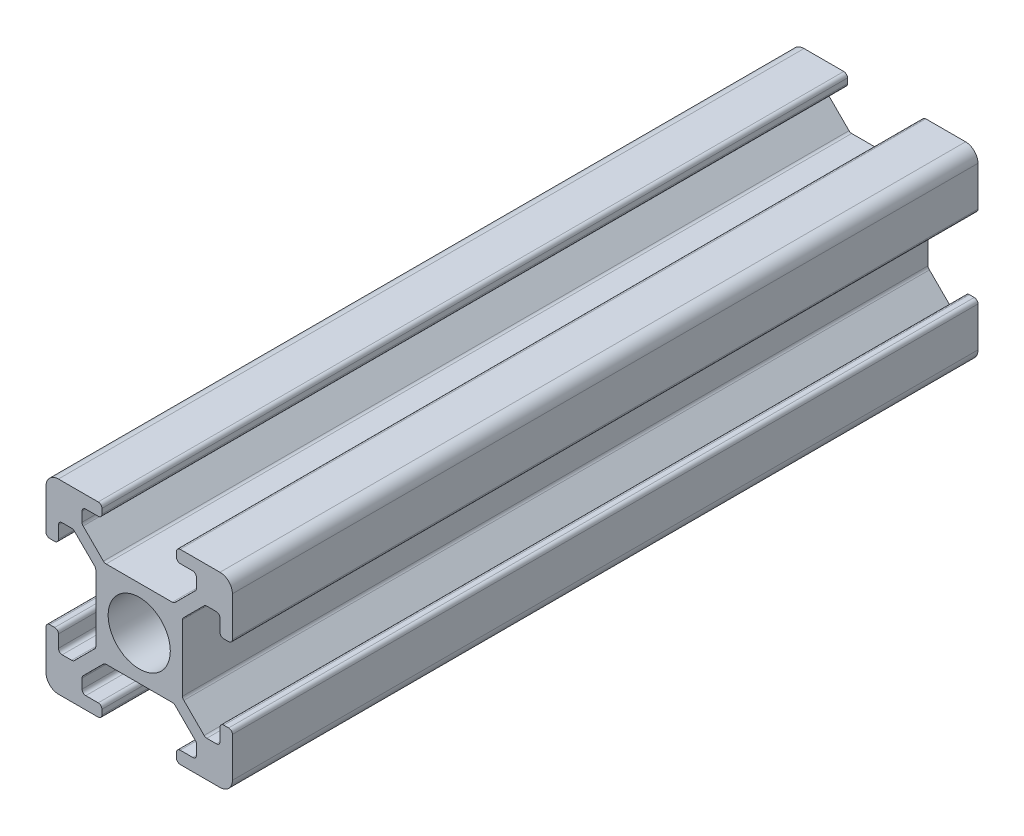
SolidWorks part; units mm, degrees
ref_plane "Front Plane" through (0, 0, 0) normal (0, 0, 1) x (1, 0, 0)
ref_plane "Top Plane" through (0, 0, 0) normal (0, 1, 0) x (1, 0, 0)
ref_plane "Right Plane" through (0, 0, 0) normal (1, 0, 0) x (0, 0, -1)
sketch "Sketch1" plane through (0, 0, 0) normal (0, 0, 1) x (1, 0, 0)
  line L0 (0.9971, -0.011) -> (4.1971, -0.011)
  line L1 (14.9971, 0.989) -> (14.9971, 4.189)
  line L2 (13.9971, 14.989) -> (10.7971, 14.989)
  line L3 (-0.0029, 13.989) -> (-0.0029, 10.789)
  line L4 (4.4971, 0.289) -> (4.4971, 0.689)
  line L5 (10.4971, 0.289) -> (10.4971, 0.689)
  line L6 (4.4971, 14.689) -> (4.4971, 14.289)
  line L7 (10.4971, 14.689) -> (10.4971, 14.289)
  line L8 (4.1971, 14.989) -> (0.9971, 14.989)
  line L9 (10.7971, -0.011) -> (13.9971, -0.011)
  line L10 (0.9971, 4.189) -> (0.9971, 3.189)
  line L11 (0.9971, 10.789) -> (0.9971, 11.7902)
  line L12 (14.6971, 10.5) -> (14.3, 10.5)
  line L13 (14.6971, 4.489) -> (14.3053, 4.489)
  line L14 (0.2971, 4.489) -> (0.6971, 4.489)
  line L15 (0.2971, 10.489) -> (0.6971, 10.489)
  line L16 (-0.0029, 4.189) -> (-0.0029, 0.989)
  line L17 (14.9971, 10.8) -> (14.9971, 13.989)
  line L18 (14, 10.8) -> (14, 11.8)
  line L19 (14.0053, 4.189) -> (14.0053, 3.189)
  line L20 (4.8302, 10.985) -> (10.1675, 10.985)
  line L21 (10.9699, 10.1634) -> (10.9699, 4.8261)
  line L22 (10.1715, 3.9947) -> (4.8343, 3.9947)
  line L23 (4.0029, 4.8261) -> (4.0029, 10.1634)
  line L24 (4.1971, 13.989) -> (3.1971, 13.989)
  line L25 (10.7971, 13.989) -> (11.7988, 13.989)
  line L26 (4.1971, 0.989) -> (3.1971, 0.989)
  line L27 (10.7971, 0.989) -> (11.8086, 0.989)
  line L28 (1.2971, 12.0902) -> (2.0579, 12.0902)
  line L29 (2.8971, 13.689) -> (2.8971, 12.9204)
  line L30 (1.2971, 2.889) -> (2.0658, 2.889)
  line L31 (2.8971, 1.289) -> (2.8971, 2.0576)
  line L32 (4.6181, 11.0728) -> (2.9867, 12.7042)
  line L33 (3.9121, 10.3808) -> (2.2729, 12.0018)
  line L34 (10.3796, 11.0728) -> (12.011, 12.7042)
  line L35 (11.0879, 10.3808) -> (12.7192, 12.0121)
  line L36 (11.0891, 4.6099) -> (12.7204, 2.9786)
  line L37 (10.3877, 3.9052) -> (12.0191, 2.2738)
  line L38 (4.6181, 3.9052) -> (2.9867, 2.2738)
  line L39 (3.9133, 4.6099) -> (2.282, 2.9786)
  line L40 (12.0988, 13.689) -> (12.0988, 12.9163)
  line L41 (13.7, 12.1) -> (12.9314, 12.1)
  line L42 (13.7053, 2.889) -> (12.9366, 2.889)
  line L43 (12.1086, 1.289) -> (12.1086, 2.0576)
  circle A0 centre (7.5, 7.5) radius 2.5
  arc A1 (0.9971, -0.011) -> (-0.0029, 0.989) centre (0.9971, 0.989) cw
  arc A2 (13.9971, -0.011) -> (14.9971, 0.989) centre (13.9971, 0.989) ccw
  arc A3 (14.9971, 13.989) -> (13.9971, 14.989) centre (13.9971, 13.989) ccw
  arc A4 (0.9971, 14.989) -> (-0.0029, 13.989) centre (0.9971, 13.989) ccw
  arc A5 (10.4971, 0.289) -> (10.7971, -0.011) centre (10.7971, 0.289) ccw
  arc A6 (10.4971, 0.689) -> (10.7971, 0.989) centre (10.7971, 0.689) cw
  arc A7 (4.4971, 0.289) -> (4.1971, -0.011) centre (4.1971, 0.289) cw
  arc A8 (4.4971, 0.689) -> (4.1971, 0.989) centre (4.1971, 0.689) ccw
  arc A9 (0.6971, 4.489) -> (0.9971, 4.189) centre (0.6971, 4.189) cw
  arc A10 (0.2971, 4.489) -> (-0.0029, 4.189) centre (0.2971, 4.189) ccw
  arc A11 (0.6971, 10.489) -> (0.9971, 10.789) centre (0.6971, 10.789) ccw
  arc A12 (0.2971, 10.489) -> (-0.0029, 10.789) centre (0.2971, 10.789) cw
  arc A13 (4.4971, 14.289) -> (4.1971, 13.989) centre (4.1971, 14.289) cw
  arc A14 (4.1971, 14.989) -> (4.4971, 14.689) centre (4.1971, 14.689) cw
  arc A15 (10.4971, 14.289) -> (10.7971, 13.989) centre (10.7971, 14.289) ccw
  arc A16 (10.7971, 14.989) -> (10.4971, 14.689) centre (10.7971, 14.689) ccw
  arc A17 (14.3053, 4.489) -> (14.0053, 4.189) centre (14.3053, 4.189) ccw
  arc A18 (14.9971, 4.189) -> (14.6971, 4.489) centre (14.6971, 4.189) ccw
  arc A19 (14.3, 10.5) -> (14, 10.8) centre (14.3, 10.8) cw
  arc A20 (14.9971, 10.8) -> (14.6971, 10.5) centre (14.6971, 10.8) cw
  arc A21 (11.7988, 13.989) -> (12.0988, 13.689) centre (11.7988, 13.689) cw
  arc A22 (14, 11.8) -> (13.7, 12.1) centre (13.7, 11.8) ccw
  arc A23 (14.0053, 3.189) -> (13.7053, 2.889) centre (13.7053, 3.189) cw
  arc A24 (11.8086, 0.989) -> (12.1086, 1.289) centre (11.8086, 1.289) ccw
  arc A25 (3.1971, 0.989) -> (2.8971, 1.289) centre (3.1971, 1.289) cw
  arc A26 (0.9971, 3.189) -> (1.2971, 2.889) centre (1.2971, 3.189) ccw
  arc A27 (0.9971, 11.7902) -> (1.2971, 12.0902) centre (1.2971, 11.7902) cw
  arc A28 (3.1971, 13.989) -> (2.8971, 13.689) centre (3.1971, 13.689) ccw
  arc A29 (10.3796, 11.0728) -> (10.1675, 10.985) centre (10.1675, 11.285) cw
  arc A30 (12.0988, 12.9163) -> (12.011, 12.7042) centre (11.7988, 12.9163) cw
  arc A31 (4.6181, 11.0728) -> (4.8302, 10.985) centre (4.8302, 11.285) ccw
  arc A32 (12.9314, 12.1) -> (12.7192, 12.0121) centre (12.9314, 11.8) ccw
  arc A33 (10.9699, 10.1634) -> (11.0879, 10.3808) centre (11.2692, 10.1417) cw
  arc A34 (11.0891, 4.6099) -> (10.9699, 4.8261) centre (11.269, 4.85) cw
  arc A35 (12.9366, 2.889) -> (12.7204, 2.9786) centre (12.9366, 3.1947) cw
  arc A36 (12.1086, 2.0576) -> (12.0191, 2.2738) centre (11.8029, 2.0576) ccw
  arc A37 (2.8971, 2.0576) -> (2.9867, 2.2738) centre (3.2029, 2.0576) cw
  arc A38 (10.3877, 3.9052) -> (10.1715, 3.9947) centre (10.1715, 3.689) ccw
  arc A39 (4.6181, 3.9052) -> (4.8343, 3.9947) centre (4.8343, 3.689) cw
  arc A40 (2.0658, 2.889) -> (2.282, 2.9786) centre (2.0658, 3.1947) ccw
  arc A41 (3.9133, 4.6099) -> (4.0029, 4.8261) centre (3.6971, 4.8261) ccw
  arc A42 (3.9121, 10.3808) -> (4.0029, 10.1634) centre (3.6971, 10.1634) cw
  arc A43 (2.8971, 12.9204) -> (2.9867, 12.7042) centre (3.2029, 12.9204) ccw
  arc A44 (2.0579, 12.0902) -> (2.2729, 12.0018) centre (2.0579, 11.7845) cw
extrude "Boss-Extrude1" add sketch "Sketch1" along normal blind 60
